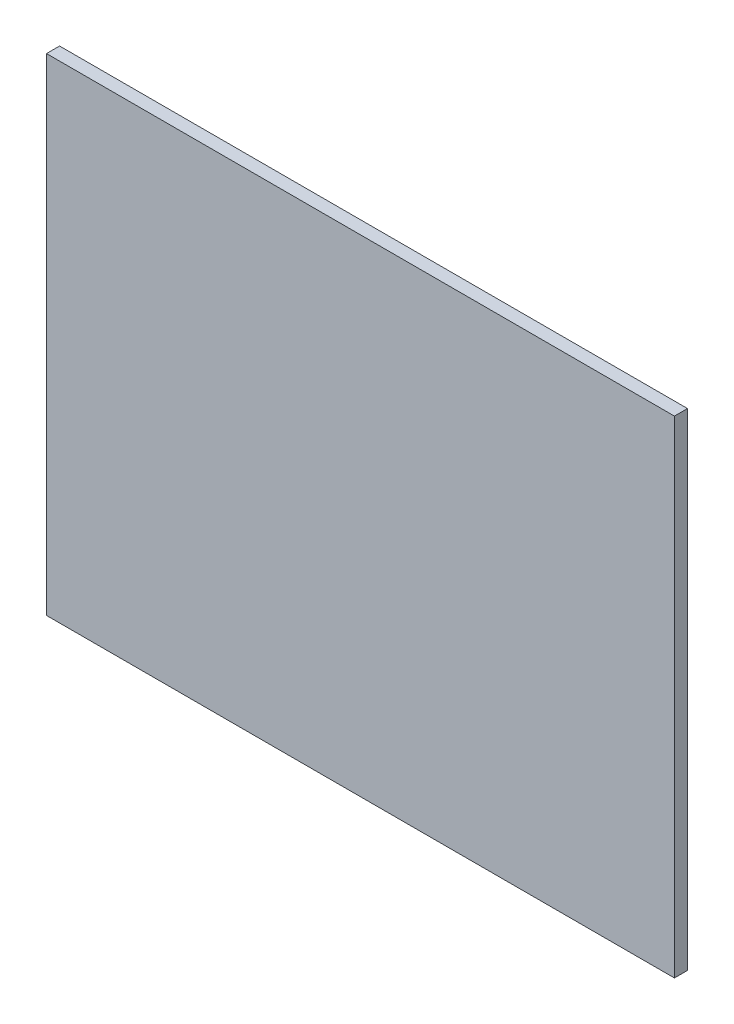
SolidWorks part; units mm, degrees
ref_plane "Front" through (0, 0, 0) normal (0, 0, 1) x (1, 0, 0)
ref_plane "Top" through (0, 0, 0) normal (0, 1, 0) x (1, 0, 0)
ref_plane "Right" through (0, 0, 0) normal (1, 0, 0) x (0, 0, -1)
sketch "Sketch1" plane through (0, 0, 0) normal (0, 0, 1) x (1, 0, 0)
  line L1 (-77.4595, 37.9426) -> (74.9405, 37.9426)
  line L2 (-77.4595, 37.9426) -> (-77.4595, -80.1674)
  line L3 (-77.4595, -80.1674) -> (74.9405, -80.1674)
  line L4 (74.9405, 37.9426) -> (74.9405, -80.1674)
  dimension "D1" = 152.4
  dimension "D2" = 118.11
extrude "Boss-Extrude1" add sketch "Sketch1" along normal blind 3.175
